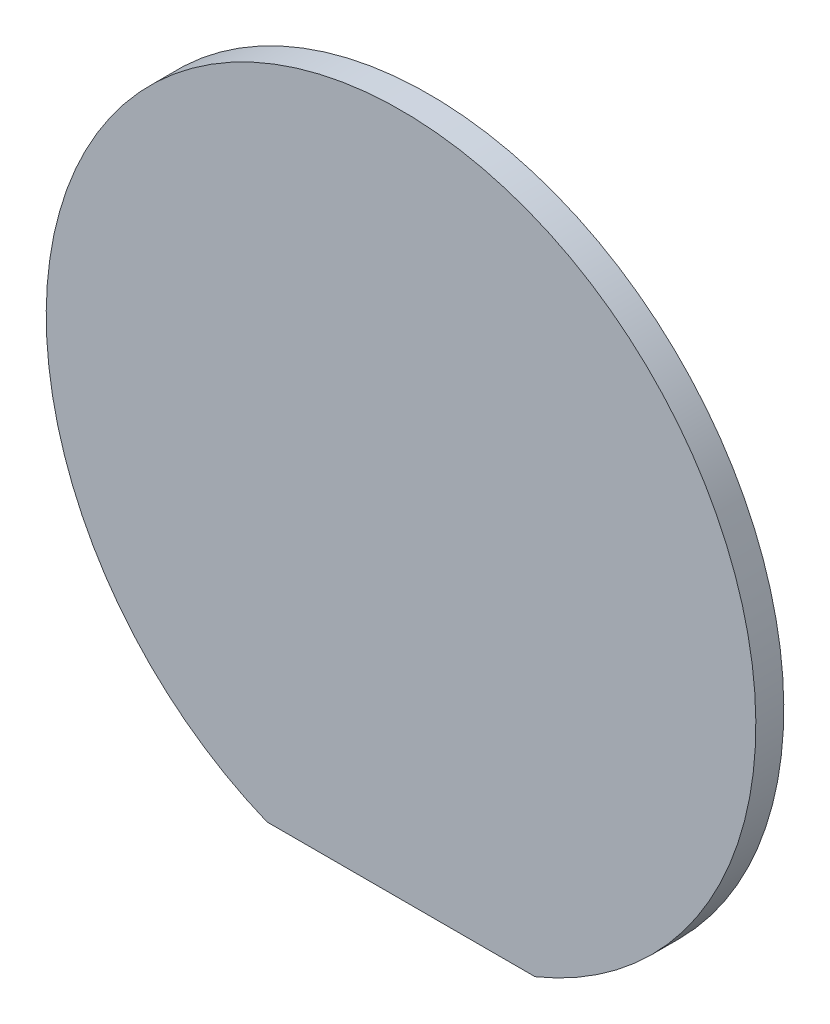
SolidWorks part; units mm, degrees
ref_plane "前视基准面" through (0, 0, 0) normal (0, 0, 1) x (1, 0, 0)
ref_plane "上视基准面" through (0, 0, 0) normal (0, 1, 0) x (1, 0, 0)
ref_plane "右视基准面" through (0, 0, 0) normal (1, 0, 0) x (0, 0, -1)
sketch "草图1" plane through (0, 0, 0) normal (0, 0, 1) x (1, 0, 0)
  circle A0 centre (0, 0) radius 12.7
  dimension "D1" = 25.4
extrude "凸台-拉伸1" add sketch "草图1" along normal blind 1
sketch "草图2" plane through (0, 0, 1) normal (0, 0, 1) x (1, 0, 0)
  line L0 (-5.8873, -11.76) -> (7.7033, -11.76)
  line L1 (-5.8873, -11.76) -> (-5.8873, -13.6858)
  line L2 (-5.8873, -13.6858) -> (7.7033, -13.6858)
  line L3 (7.7033, -13.6858) -> (7.7033, -11.76)
  dimension "D1" = 11.76
extrude "切除-拉伸1" cut sketch "草图2" against normal through all
